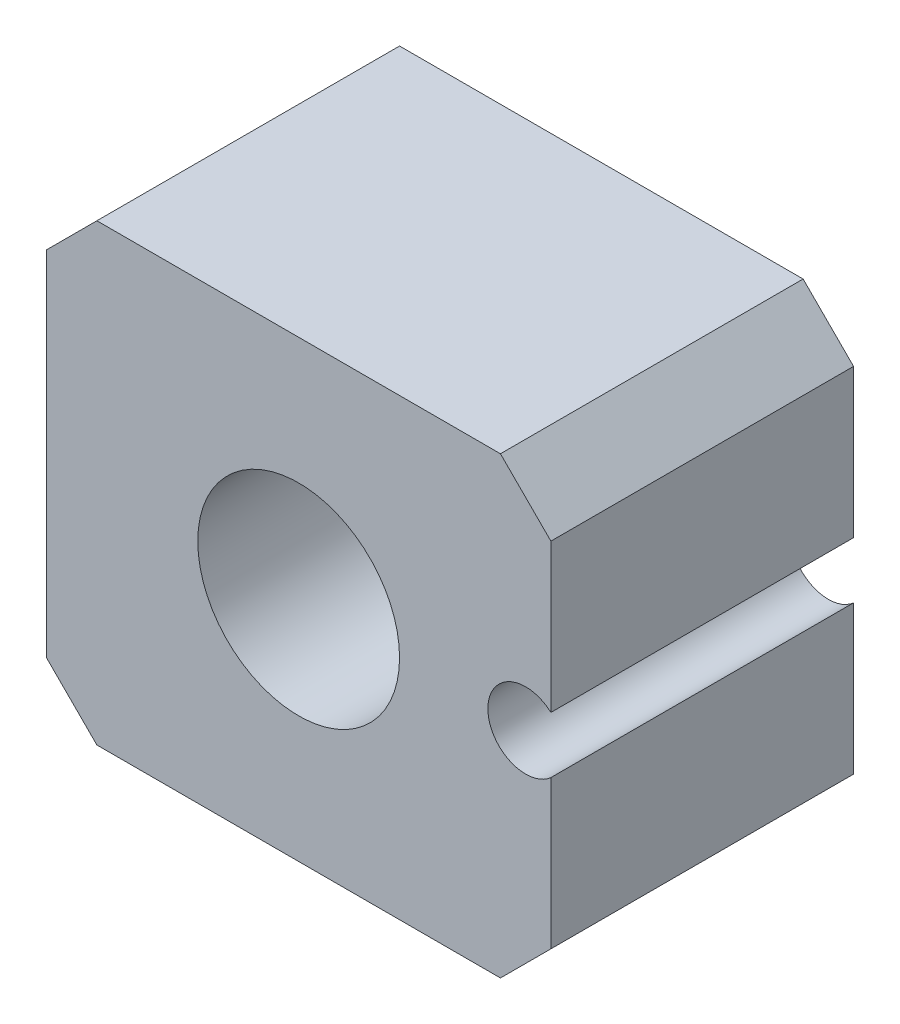
SolidWorks part; units mm, degrees
ref_plane "Front Plane" through (0, 0, 0) normal (0, 0, 1) x (1, 0, 0)
ref_plane "Top Plane" through (0, 0, 0) normal (0, 1, 0) x (1, 0, 0)
ref_plane "Right Plane" through (0, 0, 0) normal (1, 0, 0) x (0, 0, -1)
sketch "Sketch1" plane through (0, 0, 0) normal (0, 0, 1) x (1, 0, 0)
  line L0 (-10, 9) -> (-10, -9)
  line L1 (-10, 9) -> (10, 9)
  line L2 (-10, -9) -> (10, -9)
  line L3 (10, 9) -> (10, -9)
  line L4 (-10, 9) -> (10, -9) construction
  dimension "D1" = 20
  dimension "D2" = 18
extrude "Boss-Extrude1" add sketch "Sketch1" along normal blind 12
sketch "Sketch2" plane through (0, 0, 12) normal (0, 0, 1) x (1, 0, 0)
  line L1 (9, 0) -> (10, 0) construction
  line L2 (10, -9) -> (10, 9) construction
  circle A0 centre (9, 0) radius 1.5
  circle A1 centre (0, 0) radius 4
  dimension "D1" = 3
  dimension "D3" = 8
  dimension "D2" = 1
extrude "Cut-Extrude1" cut sketch "Sketch2" against normal through all
chamfer "Chamfer1" distance 2 angle 45 4 edges at (-10, 9, 6) (-10, -9, 6) (10, -9, 6) (10, 9, 6)
